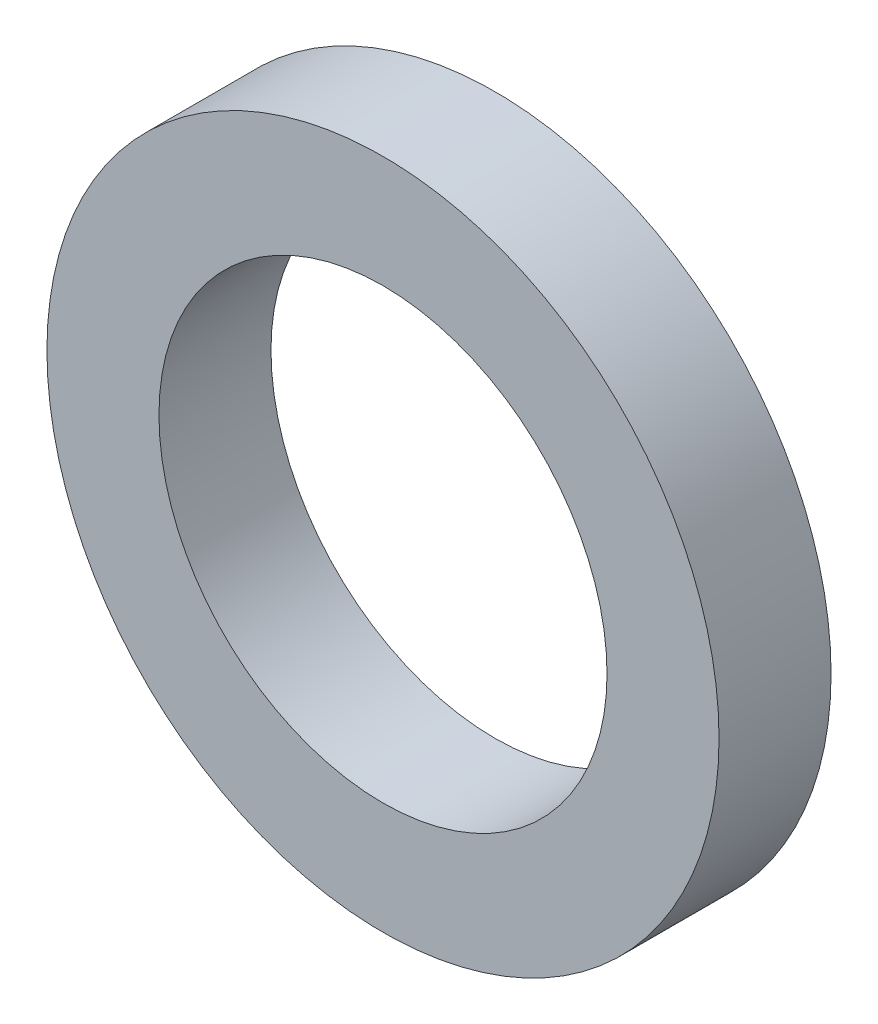
SolidWorks part; units mm, degrees
ref_plane "Front Plane" through (0, 0, 0) normal (0, 0, 1) x (1, 0, 0)
ref_plane "Top Plane" through (0, 0, 0) normal (0, 1, 0) x (1, 0, 0)
ref_plane "Right Plane" through (0, 0, 0) normal (1, 0, 0) x (0, 0, -1)
sketch "Sketch1" plane through (0, 0, 0) normal (0, 0, 1) x (1, 0, 0)
  circle A0 centre (0, 0) radius 15
  circle A1 centre (0, 0) radius 10
  dimension "D1" = 20
  dimension "D2" = 30
extrude "Boss-Extrude1" add sketch "Sketch1" along normal blind 5
